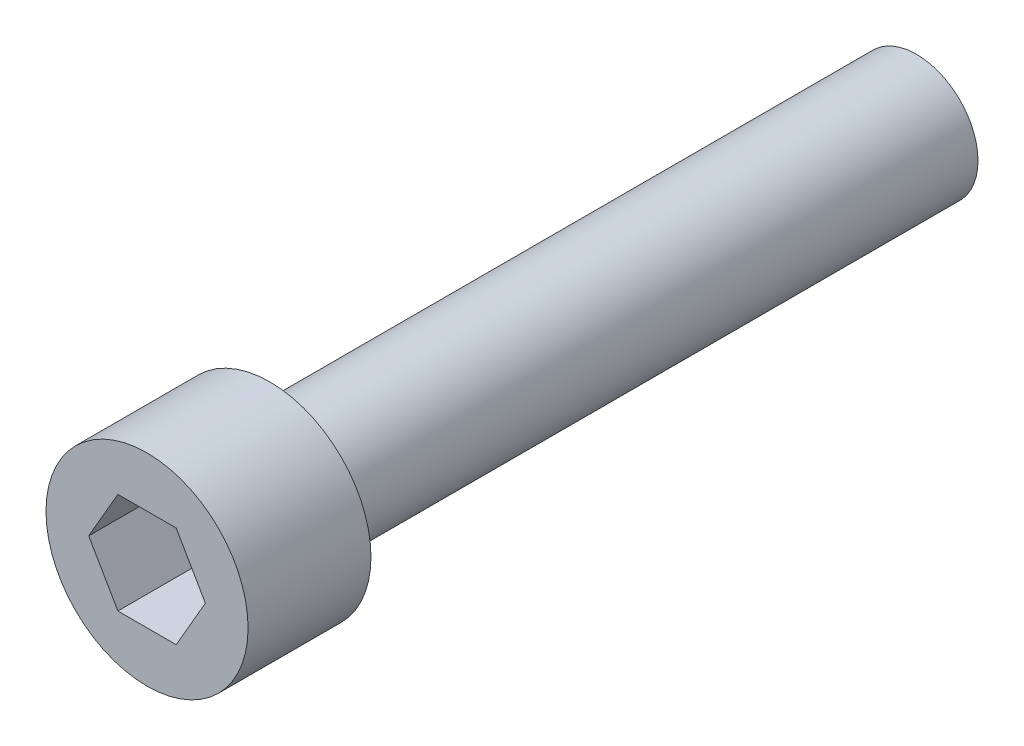
SolidWorks part; units mm, degrees
material "Cast Alloy Steel"
ref_plane "Front Plane" through (0, 0, 0) normal (0, 0, 1) x (1, 0, 0)
ref_plane "Top Plane" through (0, 0, 0) normal (0, 1, 0) x (1, 0, 0)
ref_plane "Right Plane" through (0, 0, 0) normal (1, 0, 0) x (0, 0, -1)
sketch "Sketch1" plane through (0, 0, 0) normal (0, 0, 1) x (1, 0, 0)
  circle A0 centre (0, 0) radius 2.413
  dimension "D1" = 4.826
extrude "Boss-Extrude1" add sketch "Sketch1" along normal blind 25.4
sketch "Sketch2" plane through (0, 0, 25.4) normal (0, 0, 1) x (1, 0, 0)
  circle A0 centre (0, 0) radius 3.9688
  dimension "D1" = 7.9375
extrude "Boss-Extrude2" add sketch "Sketch2" along normal blind 4.826
sketch "Sketch3" plane through (0, 0, 30.226) normal (0, 0, 1) x (1, 0, 0)
  line L1 (2.2914, 0) -> (1.1457, 1.9844)
  line L2 (1.1457, 1.9844) -> (-1.1457, 1.9844)
  line L3 (-1.1457, 1.9844) -> (-2.2914, 0)
  line L4 (-2.2914, 0) -> (-1.1457, -1.9844)
  line L5 (-1.1457, -1.9844) -> (1.1457, -1.9844)
  line L6 (1.1457, -1.9844) -> (2.2914, 0)
  circle A0 centre (0, 0) radius 1.9844 construction
  dimension "D1" = 3.9688
extrude "Cut-Extrude1" cut sketch "Sketch3" against normal blind 3.81
